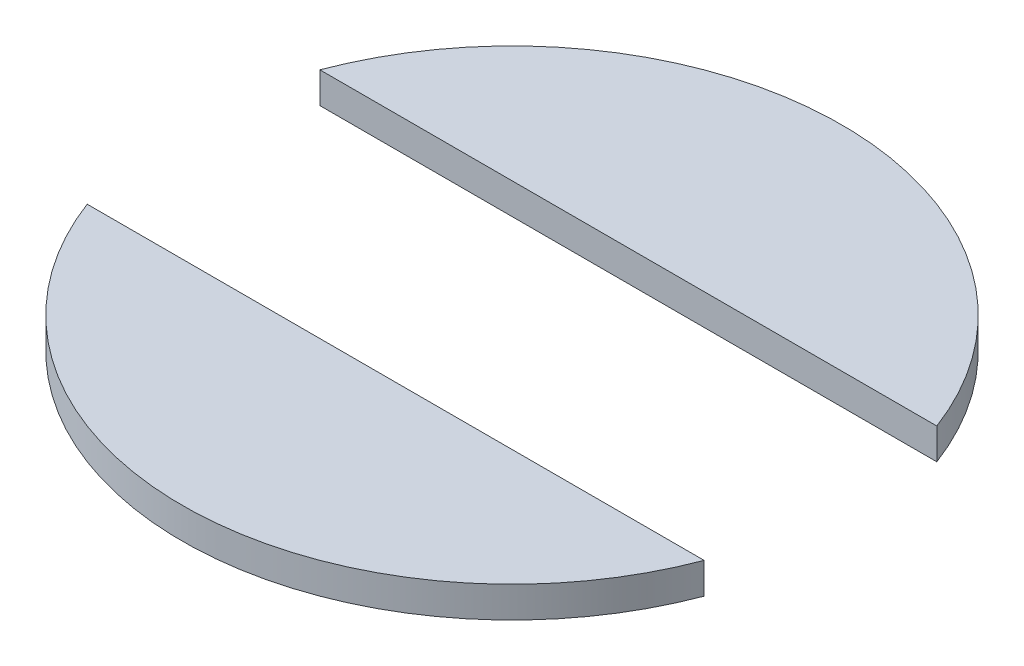
SolidWorks part; units mm, degrees
ref_plane "Front Plane" through (0, 0, 0) normal (0, 0, 1) x (1, 0, 0)
ref_plane "Top Plane" through (0, 0, 0) normal (0, 1, 0) x (1, 0, 0)
ref_plane "Right Plane" through (0, 0, 0) normal (1, 0, 0) x (0, 0, -1)
sketch "Sketch1" plane through (0, 0, 0) normal (0, 1, 0) x (1, 0, 0)
  line L1 (2.125, -0.75) -> (-2.125, -0.75)
  line L2 (2.125, -0.75) -> (2.125, 0.75)
  line L3 (2.125, 0.75) -> (-2.125, 0.75)
  line L4 (-2.125, -0.75) -> (-2.125, 0.75)
  circle A0 centre (0, 0) radius 2.125
  point P7 (-2.125, 0)
  dimension "D1" = 4.25
  dimension "D2" = 1.5
extrude "Boss-Extrude1" add sketch "Sketch1" along normal blind 0.2 contours L1 A0 | L3 A0
